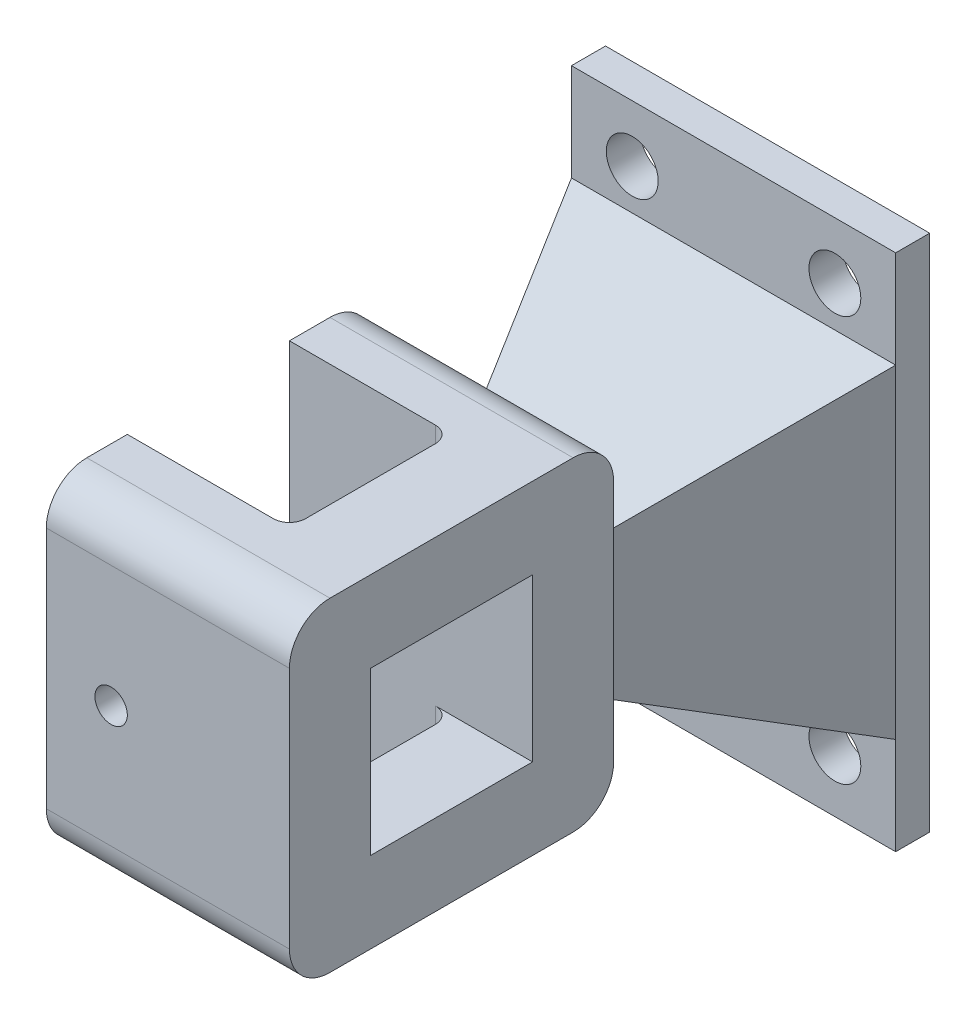
SolidWorks part; units mm, degrees
ref_plane "정면" through (0, 0, 0) normal (0, 0, 1) x (1, 0, 0)
ref_plane "윗면" through (0, 0, 0) normal (0, 1, 0) x (1, 0, 0)
ref_plane "우측면" through (0, 0, 0) normal (1, 0, 0) x (0, 0, -1)
sketch "스케치1" plane through (0, 0, 0) normal (0, 0, 1) x (1, 0, 0)
  line L1 (12.5, -25) -> (-12.5, -25)
  line L2 (12.5, -25) -> (12.5, 25)
  line L3 (12.5, 25) -> (-12.5, 25) construction
  line L4 (-12.5, -25) -> (-12.5, 25) construction
  line L5 (12.5, -25) -> (-12.5, 25) construction
  line L6 (12.5, 25) -> (-12.5, -25) construction
  line L7 (20, -32) -> (-20, -32)
  line L8 (20, -32) -> (20, 32)
  line L9 (20, 32) -> (-20, 32)
  line L10 (-20, -32) -> (-20, 32)
  line L11 (20, -32) -> (-20, 32) construction
  line L12 (20, 32) -> (-20, -32) construction
  circle A0 centre (-12.5, 25) radius 3.2
  circle A1 centre (12.5, 25) radius 3.2
  circle A2 centre (12.5, -25) radius 3.2
  circle A3 centre (-12.5, -25) radius 3.2
  circle A4 centre (-12.5, 25) radius 5.5 construction
  point P0 (0, 0)
  point P6 (0, 0)
  dimension "D5" = 6.4
  dimension "D6" = 11
  dimension "D1" = 50
  dimension "D2" = 25
  dimension "D3" = 40
  dimension "D4" = 64
extrude "보스-돌출1" add sketch "스케치1" along normal blind 4.2
sketch "스케치2" plane through (0, 0, 0) normal (1, 0, 0) x (0, 0, -1)
  line L0 (0, 0) -> (-57.25, 0) construction
  line L1 (-57.25, 0) -> (-58.5, 0) construction
  line L2 (-39.5, -11.3934) -> (-39.5, 11.3934) construction
  line L4 (-39, -10) -> (-59, -10)
  line L5 (-39, -10) -> (-39, 10)
  line L6 (-39, 10) -> (-59, 10)
  line L7 (-59, -10) -> (-59, 10)
  line L8 (-39, -10) -> (-59, 10) construction
  line L9 (-39, 10) -> (-59, -10) construction
  circle A0 centre (-49, 0) radius 16
  point P7 (-39.5, 0)
  dimension "D5" = 32
  dimension "D1" = 57.25
  dimension "D2" = 1.25
  dimension "D3" = 19
  dimension "D4" = 9.5
  dimension "D6" = 20
  dimension "D7" = 20
extrude "보스-돌출2" add sketch "스케치2" along normal blind 10 and the other way blind 20 separate body
sketch "스케치3" plane through (-20, 0, 0) normal (-1, 0, 0) x (0, 0, 1)
  line L1 (59, -16) -> (39, -16)
  line L2 (59, -16) -> (59, 16)
  line L3 (59, 16) -> (39, 16)
  line L4 (39, -16) -> (39, 16)
  line L5 (59, -16) -> (39, 16) construction
  line L6 (59, 16) -> (39, -16) construction
  point P0 (49, 0)
  dimension "D1" = 20
  dimension "D2" = 32
extrude "컷-돌출1" cut sketch "스케치3" against normal blind 20
sketch "스케치5" plane through (0, 0, 0) normal (0, 1, 0) x (1, 0, 0)
  line L0 (-20, -4.2) -> (-7, -33)
  line L1 (10, -33) -> (-20, -33) construction
  line L2 (-7, -33) -> (7, -33)
  line L4 (7, -33) -> (20, -4.2)
  line L5 (20, -4.2) -> (-20, -4.2)
  line L6 (0, 0) -> (0, -33) construction
  line L7 (20, 0) -> (-20, 0) construction
  line L8 (-13.8058, -8.2) -> (-4, -8.2)
  line L9 (-4, -8.2) -> (-4, -29.9237)
  line L10 (-4, -29.9237) -> (-13.8058, -8.2)
  line L11 (4, -29.9237) -> (13.8058, -8.2)
  line L12 (4, -8.2) -> (4, -29.9237)
  line L13 (13.8058, -8.2) -> (4, -8.2)
  dimension "D1" = 14
  dimension "D2" = 4
  dimension "D3" = 4
  dimension "D4" = 4
extrude "보스-돌출3" add sketch "스케치5" along normal mid plane 6
sketch "스케치7" plane through (0, 0, 33) normal (0, 0, 1) x (1, 0, 0)
  line L4 (-7, -3) -> (7, -3)
  line L5 (7, -3) -> (7, 3)
  line L6 (7, 3) -> (-7, 3)
  line L7 (-7, 3) -> (-7, -3)
  line L8 (-7, -3) -> (7, -3)
  line L9 (7, -3) -> (7, 3)
  line L10 (7, 3) -> (-7, 3)
  line L11 (-7, 3) -> (-7, -3)
  dimension "D1" = 0
extrude "보스-돌출4" add sketch "스케치7" along normal up to surface (0.2838 mm away)
sketch "스케치8" plane through (0, 0, 0) normal (1, 0, 0) x (0, 0, -1)
  line L0 (-4.2, 20) -> (-33, 7)
  line L1 (-33, 7) -> (-33, -7)
  line L2 (-33, -7) -> (-4.2, -20)
  line L3 (-4.2, -20) -> (-4.2, 20)
  line L4 (-33, 0) -> (0, 0) construction
  line L5 (-8.2, 13.8058) -> (-8.2, 4)
  line L6 (-8.2, 4) -> (-29.9237, 4)
  line L7 (-29.9237, 4) -> (-8.2, 13.8058)
  line L8 (-8.2, -4) -> (-29.9237, -4)
  line L9 (-8.2, -13.8058) -> (-8.2, -4)
  line L10 (-29.9237, -4) -> (-8.2, -13.8058)
  line L11 (-4.2, -32) -> (-4.2, -3) construction
  dimension "D1" = 4
  dimension "D2" = 4
  dimension "D3" = 4
  dimension "D4" = 14
  dimension "D5" = 33
  dimension "D6" = 20
  dimension "D7" = 40
extrude "보스-돌출5" add sketch "스케치8" along normal mid plane 6
sketch "스케치9" plane through (0, 0, 33) normal (0, 0, 1) x (1, 0, 0)
  line L1 (3, -7) -> (-3, -7)
  line L2 (3, -7) -> (3, 7)
  line L3 (3, 7) -> (-3, 7)
  line L4 (-3, -7) -> (-3, 7)
  line L5 (3, -7) -> (-3, 7) construction
  line L6 (3, 7) -> (-3, -7) construction
  point P0 (0, 0)
extrude "보스-돌출6" add sketch "스케치9" along normal up to surface
sketch "스케치10" plane through (0, 0, 4.2) normal (0, 0, 1) x (1, 0, 0)
  line L0 (20, 3) -> (20, 32) construction
  line L1 (20, 20) -> (-20, 20)
  line L2 (20, 20) -> (20, -20)
  line L3 (20, -20) -> (-20, -20)
  line L4 (-20, 20) -> (-20, -20)
  line L5 (-20, -32) -> (-20, -3) construction
  line L6 (3, 20) -> (-3, 20) construction
  line L7 (3, -20) -> (-3, -20) construction
ref_plane "평면1" through (0, 0, 33) normal (0, 0, 1) x (1, 0, 0)
sketch "스케치11" plane through (0, 0, 33) normal (0, 0, 1) x (1, 0, 0)
  line L0 (3, 7) -> (-3, 7) construction
  line L1 (7, 7) -> (-7, 7)
  line L2 (7, 7) -> (7, -7)
  line L3 (7, -7) -> (-7, -7)
  line L4 (-7, 7) -> (-7, -7)
  line L5 (3, -7) -> (-3, -7) construction
  line L6 (7, 0) -> (7, -3) construction
  line L7 (-7, 3) -> (-7, 0) construction
  point P4 (0, 0)
loft "로프트1" add profiles "스케치10", "스케치11"
sketch "스케치12" plane through (0, 0, 33) normal (0, 0, 1) x (1, 0, 0)
  line L0 (-7, 7) -> (-7, 3) construction
  line L1 (7, 7) -> (-7, 7)
  line L2 (7, 7) -> (7, -7)
  line L3 (7, -7) -> (-7, -7)
  line L4 (-7, 7) -> (-7, -7)
  line L5 (-3, 7) -> (-7, 7) construction
  line L6 (7, 3) -> (7, 7) construction
  line L7 (-7, -7) -> (-3, -7) construction
extrude "보스-돌출8" add sketch "스케치12" along normal up to surface (6 mm away) up to face at (-2.5, 0, 39)
sketch "스케치14" plane through (10, 0, 0) normal (1, 0, 0) x (0, 0, -1)
  line L1 (-29, 20) -> (-69, 20)
  line L2 (-29, 20) -> (-29, -20)
  line L3 (-29, -20) -> (-69, -20)
  line L4 (-69, 20) -> (-69, -20)
  line L5 (-39, 10) -> (-59, 10)
  line L6 (-39, 10) -> (-39, -10)
  line L7 (-39, -10) -> (-59, -10)
  line L8 (-59, 10) -> (-59, -10)
  circle A0 centre (-49, 0) radius 16 construction
  dimension "D1" = 20
  dimension "D2" = 20
  dimension "D3" = 20
  dimension "D4" = 20
extrude "보스-돌출10" add sketch "스케치14" against normal up to surface (10 mm away) up to face at (0, -12.1225, 49)
sketch "스케치15" plane through (-20, 0, 0) normal (-1, 0, 0) x (0, 0, 1)
  line L0 (69, -20) -> (29, -20) construction
  line L1 (69, 20) -> (59, 20)
  line L2 (69, 20) -> (69, -20)
  line L3 (69, -20) -> (59, -20)
  line L4 (59, 20) -> (59, -20)
  line L5 (29, 20) -> (69, 20) construction
  line L6 (39, 20) -> (29, 20)
  line L7 (39, 20) -> (39, -20)
  line L8 (39, -20) -> (29, -20)
  line L9 (29, 20) -> (29, -20)
  line L10 (39, -12.49) -> (39, 12.49) construction
  line L11 (59, 12.49) -> (59, -12.49) construction
extrude "보스-돌출11" add sketch "스케치15" against normal up to surface (20 mm away) up to face at (0, 0, 43.7008)
sketch "스케치4" plane through (0, 0, 39) normal (0, 0, 1) x (1, 0, 0)
  circle A0 centre (-12, 0) radius 2
  dimension "D2" = 4
  dimension "D1" = 12
extrude "컷-돌출2" cut sketch "스케치4" against normal up to surface and the other way up to surface
fillet "필렛2" radius 5 4 edges at (-5, 20, 69) (-5, -20, 69) (-5, -20, 29) (-5, 20, 29)
fillet "필렛3" radius 2 4 edges at (0, 15, 59) (0, 15, 39) (0, -15, 39) (0, -15, 59)
